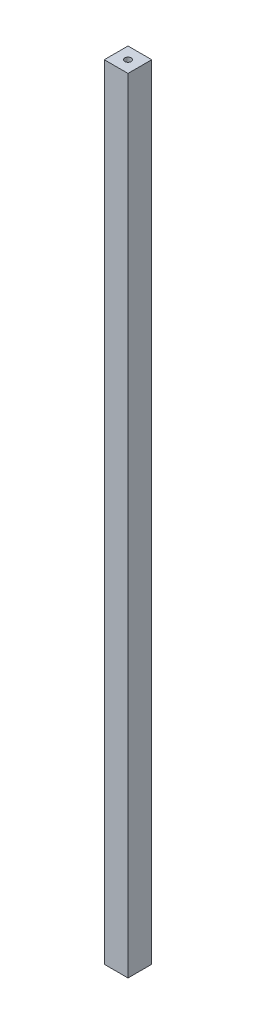
SolidWorks part; units mm, degrees
material "Plain Carbon Steel"
ref_plane "Front Plane" through (0, 0, 0) normal (0, 0, 1) x (1, 0, 0)
ref_plane "Top Plane" through (0, 0, 0) normal (0, 1, 0) x (1, 0, 0)
ref_plane "Right Plane" through (0, 0, 0) normal (1, 0, 0) x (0, 0, -1)
sketch "Sketch1" plane through (0, 0, 0) normal (0, 1, 0) x (1, 0, 0)
  line L1 (0, 0) -> (10, 0)
  line L2 (0, 0) -> (0, 10)
  line L3 (0, 10) -> (10, 10)
  line L4 (10, 0) -> (10, 10)
  dimension "D1" = 10
extrude "Boss-Extrude1" add sketch "Sketch1" along normal blind 330
hole_wizard "#6-32 Tapped Hole1" positions "Sketch2" profile "Sketch3" tap size "#6-32" standard "ANSI Inch" end condition through all
sketch "Sketch2" plane through (0, 330, 0) normal (0, 1, 0) x (1, 0, 0)
  line L0 (0, 10) -> (10, 0) construction
  line L2 (10, 10) -> (0, 0) construction
  point P13 (5, 5)
sketch "Sketch3" plane through (5, 330, -5) normal (1, 0, 0) x (0, 0, 1)
  line L0 (0, 0) -> (0, 330)
  line L1 (0, 330) -> (1.3525, 330)
  line L2 (1.3525, 330) -> (1.3525, 0)
  line L5 (1.3525, 0) -> (0, 0)
  line L11 (0, -6.35) -> (0, 107.95) construction
  dimension "Thread Major Dia." = 2.7051
  dimension "Thru Tap Drill Depth" = 330
